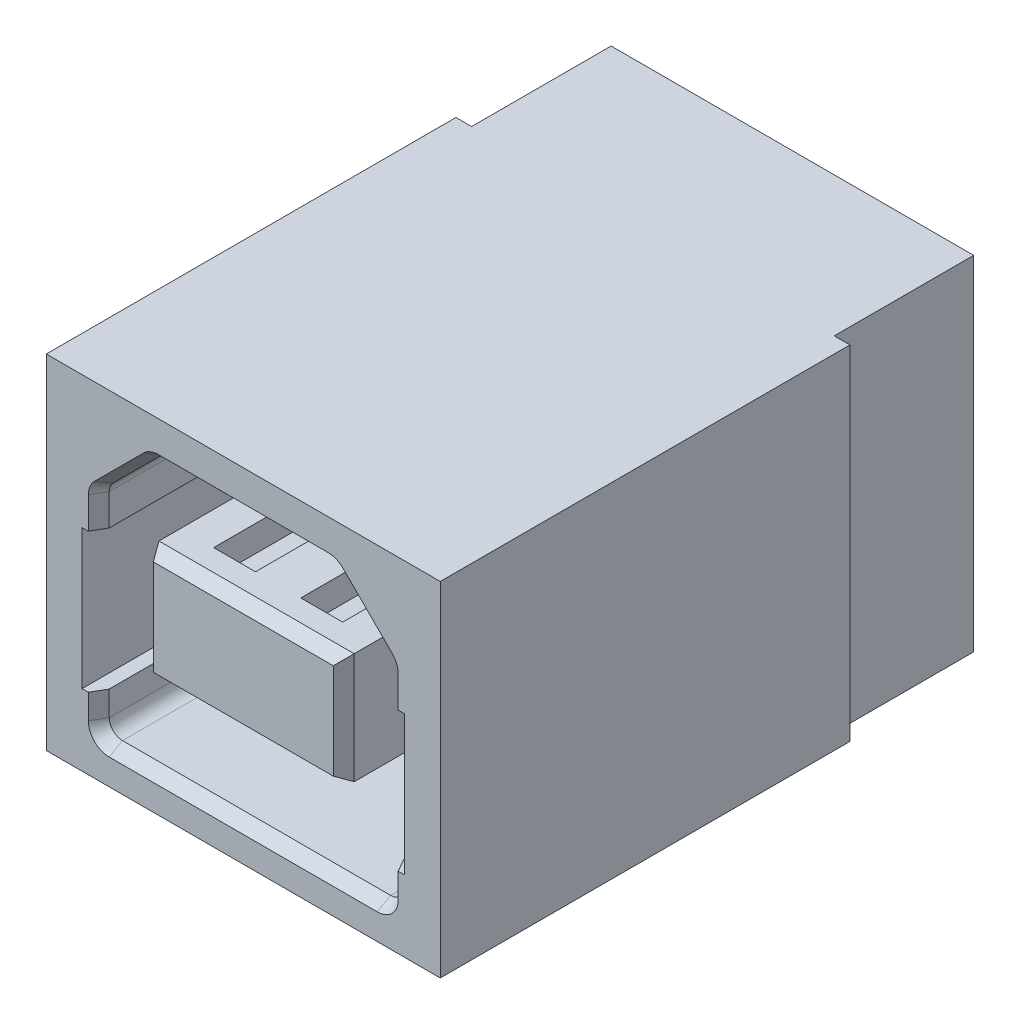
SolidWorks part; units mm, degrees
material "PTFE (general)"
ref_plane "Front Plane" through (0, 0, 0) normal (0, 0, 1) x (1, 0, 0)
ref_plane "Top Plane" through (0, 0, 0) normal (0, 1, 0) x (1, 0, 0)
ref_plane "Right Plane" through (0, 0, 0) normal (1, 0, 0) x (0, 0, -1)
ref_plane "Plane1" through (0, 0, -0.38) normal (0, 0, 1) x (1, 0, 0)
sketch "Sketch1" plane through (0, 0, -0.38) normal (0, 0, 1) x (1, 0, 0)
  line L0 (55, 0) -> (-55, 0) construction
  line L1 (-5.65, 10.25) -> (5.65, 10.25)
  line L2 (-5.65, 10.25) -> (-5.65, 0.4)
  line L3 (-5.65, 0.4) -> (5.65, 0.4)
  line L4 (5.65, 10.25) -> (5.65, 0.4)
  line L5 (0, -55) -> (0, 55) construction
  dimension "D1" = 11.3
  dimension "D2" = 10.25
  dimension "D3" = 0.4
  dimension "D4" = 5.65
extrude "Boss-Extrude1" add sketch "Sketch1" against normal blind 15.75
sketch "Sketch2" plane through (0, 10.25, 0) normal (0, 1, 0) x (1, 0, 0)
  line L0 (0, -55) -> (0, 55) construction
  line L1 (-5.65, 16.13) -> (-5.2, 16.13)
  line L2 (-5.65, 16.13) -> (-5.65, 12.13)
  line L3 (-5.65, 12.13) -> (-5.2, 12.13)
  line L4 (-5.2, 16.13) -> (-5.2, 12.13)
  line L5 (5.65, 16.13) -> (5.2, 16.13)
  line L6 (5.65, 16.13) -> (5.65, 12.13)
  line L7 (5.65, 12.13) -> (5.2, 12.13)
  line L8 (5.2, 16.13) -> (5.2, 12.13)
  dimension "D1" = 10.4
  dimension "D2" = 5.2
  dimension "D3" = 4
extrude "Cut-Extrude1" cut sketch "Sketch2" against normal blind 15.75
sketch "Sketch3" plane through (0, 0, -0.38) normal (0, 0, 1) x (1, 0, 0)
  line L0 (-5.65, 4.45) -> (5.65, 4.45) construction
  line L1 (-5.65, 10.25) -> (-5.65, 0.4) construction
  line L2 (5.65, 0.4) -> (5.65, 10.25) construction
  line L3 (55, 0) -> (-55, 0) construction
  line L4 (-4.225, 7.3526) -> (-4.225, 6.45)
  line L5 (-3.845, 1.36) -> (3.845, 1.36)
  line L6 (4.225, 1.74) -> (4.225, 2.45)
  line L7 (4.1137, 7.6213) -> (2.7063, 9.0287)
  line L8 (2.4376, 9.14) -> (-2.4376, 9.14)
  line L9 (-2.7063, 9.0287) -> (-4.1137, 7.6213)
  line L10 (0, -55) -> (0, 55) construction
  line L11 (-2.8, 5.25) -> (2.8, 5.25) construction
  line L12 (-2.8, 6.84) -> (2.8, 6.84)
  line L13 (-2.8, 6.84) -> (-2.8, 3.66)
  line L14 (-2.8, 3.66) -> (2.8, 3.66)
  line L15 (2.8, 6.84) -> (2.8, 3.66)
  line L16 (-4.225, 2.45) -> (-4.225, 1.74)
  line L17 (4.225, 6.45) -> (4.625, 6.45)
  line L19 (4.225, 2.45) -> (4.625, 2.45)
  line L20 (4.625, 6.45) -> (4.625, 2.45)
  line L21 (-4.225, 6.45) -> (-4.625, 6.45)
  line L22 (4.225, 6.45) -> (4.225, 7.3526)
  line L23 (-4.225, 2.45) -> (-4.625, 2.45)
  line L24 (-4.625, 6.45) -> (-4.625, 2.45)
  arc A0 (-4.225, 7.3526) -> (-4.1137, 7.6213) centre (-3.845, 7.3526) cw
  arc A1 (-2.4376, 9.14) -> (-2.7063, 9.0287) centre (-2.4376, 8.76) ccw
  arc A2 (2.7063, 9.0287) -> (2.4376, 9.14) centre (2.4376, 8.76) ccw
  arc A3 (4.225, 7.3526) -> (4.1137, 7.6213) centre (3.845, 7.3526) ccw
  arc A4 (3.845, 1.36) -> (4.225, 1.74) centre (3.845, 1.74) ccw
  arc A5 (-4.225, 1.74) -> (-3.845, 1.36) centre (-3.845, 1.74) ccw
  point P24 (-4.225, 7.51)
  point P31 (4.225, 7.51)
  dimension "D16" = 0.38
  dimension "D2" = 135
  dimension "D3" = 4.225
  dimension "D4" = 8.45
  dimension "D5" = 7.78
  dimension "D6" = 1.63
  dimension "D7" = 5.6
  dimension "D8" = 2.8
  dimension "D9" = 3.18
  dimension "D10" = 0.8
  dimension "D11" = 5.25
  dimension "D12" = 4.45
  dimension "D13" = 2.3
  dimension "D14" = 2.3
  dimension "D15" = 1.36
  dimension "D17" = 0.4
  dimension "D18" = 4
  dimension "D19" = 2
extrude "Cut-Extrude2" cut sketch "Sketch3" against normal blind 8.38
chamfer "Chamfer1" distance 0.38 angle 30 4 edges at (0, 3.66, -0.38) (2.8, 5.25, -0.38) (0, 6.84, -0.38) (-2.8, 5.25, -0.38)
chamfer "Chamfer2" distance 0.38 angle 30 14 edges at (4.225, 2.095, -0.38) (4.1137, 1.4713, -0.38) (0, 1.36, -0.38) (-4.1137, 1.4713, -0.38) (-4.225, 2.095, -0.38) (4.225, 6.9013, -0.38) (4.1961, 7.498, -0.38) (3.41, 8.325, -0.38) (2.583, 9.1111, -0.38) (0, 9.14, -0.38) (-2.583, 9.1111, -0.38) (-3.41, 8.325, -0.38) (-4.1961, 7.498, -0.38) (-4.225, 6.9013, -0.38)
sketch "Sketch4" plane through (0, 0.4, 0) normal (0, -1, 0) x (-1, 0, 0)
  line L0 (5.2, 16.13) -> (-5.2, 16.13) construction
  line L1 (4.25, 6) -> (3.25, 6)
  line L2 (4.25, 6) -> (4.25, 16.13)
  line L3 (4.25, 16.13) -> (3.25, 16.13)
  line L4 (3.25, 6) -> (3.25, 16.13)
  line L5 (-5.4175, 0) -> (5.4175, 0) construction
  line L6 (0.5, 7.5) -> (-0.5, 7.5)
  line L7 (0.5, 7.5) -> (0.5, 16.13)
  line L8 (0.5, 16.13) -> (-0.5, 16.13)
  line L9 (-0.5, 7.5) -> (-0.5, 16.13)
  line L10 (-3.25, 6) -> (-4.25, 6)
  line L11 (-3.25, 6) -> (-3.25, 16.13)
  line L12 (-3.25, 16.13) -> (-4.25, 16.13)
  line L13 (-4.25, 6) -> (-4.25, 16.13)
  line L14 (0, 5.4175) -> (0, -5.4175) construction
  dimension "D1" = 1
  dimension "D2" = 6
  dimension "D3" = 0.5
  dimension "D4" = 8.5
  dimension "D5" = 4.25
  dimension "D6" = 1.5
extrude "Boss-Extrude2" add sketch "Sketch4" along normal blind 0.83
ref_plane "Plane2" through (0, 0, -1.38) normal (0, 0, 1) x (1, 0, 0)
sketch "Sketch5" plane through (0, 0, -1.38) normal (0, 0, 1) x (1, 0, 0)
  line L0 (-2.8, 6.84) -> (2.8, 6.84) construction
  line L1 (-1.85, 6.84) -> (-0.65, 6.84)
  line L2 (-1.85, 6.84) -> (-1.85, 6.09)
  line L3 (-1.85, 6.09) -> (-0.65, 6.09)
  line L4 (-0.65, 6.84) -> (-0.65, 6.09)
  line L5 (-2.8, 3.66) -> (2.8, 3.66) construction
  line L6 (0.65, 6.84) -> (1.85, 6.84)
  line L7 (0.65, 6.84) -> (0.65, 6.09)
  line L8 (0.65, 6.09) -> (1.85, 6.09)
  line L9 (1.85, 6.84) -> (1.85, 6.09)
  line L10 (0.65, 3.66) -> (1.85, 3.66)
  line L11 (0.65, 3.66) -> (0.65, 4.41)
  line L12 (0.65, 4.41) -> (1.85, 4.41)
  line L13 (1.85, 3.66) -> (1.85, 4.41)
  line L14 (2.8, 3.66) -> (-2.8, 3.66) construction
  line L15 (-1.85, 3.66) -> (-0.65, 3.66)
  line L16 (-1.85, 3.66) -> (-1.85, 4.41)
  line L17 (-1.85, 4.41) -> (-0.65, 4.41)
  line L18 (-0.65, 3.66) -> (-0.65, 4.41)
  line L20 (-1.25, 6.84) -> (-1.25, 3.66) construction
  line L21 (1.25, 6.84) -> (1.25, 3.66) construction
  line L22 (0, -5.874) -> (0, 5.874) construction
  dimension "D1" = 1.2
  dimension "D2" = 1.25
  dimension "D3" = 1.25
  dimension "D4" = 0.75
extrude "Cut-Extrude3" cut sketch "Sketch5" against normal through all
sketch "Sketch6" plane through (0, 0, -16.13) normal (0, 0, -1) x (-1, 0, 0)
  line L0 (-0.5, 0.4) -> (-3.25, 0.4) construction
  line L1 (-1.85, 6.84) -> (-0.65, 6.84)
  line L2 (-1.85, 6.84) -> (-1.85, 0.4)
  line L3 (-1.85, 0.4) -> (-0.65, 0.4)
  line L4 (-0.65, 6.84) -> (-0.65, 0.4)
  line L5 (-0.65, 6.84) -> (-0.65, 6.09) construction
  line L6 (0.65, 6.84) -> (1.85, 6.84)
  line L7 (0.65, 6.84) -> (0.65, 0.4)
  line L8 (0.65, 0.4) -> (1.85, 0.4)
  line L9 (1.85, 6.84) -> (1.85, 0.4)
  line L10 (1.85, 6.84) -> (1.85, 6.09) construction
  line L11 (3.25, 0.4) -> (0.5, 0.4) construction
extrude "Cut-Extrude4" cut sketch "Sketch6" against normal blind 1.29
sketch "Sketch7" plane through (0, 0, -14.84) normal (0, 0, -1) x (-1, 0, 0)
  line L0 (-0.65, 0.4) -> (-0.65, 3.66) construction
  line L1 (1.85, 3.66) -> (0.65, 3.66) construction
  line L2 (-1.55, 2.66) -> (-1.55, 0)
  line L3 (-1.55, 0) -> (-0.95, 0)
  line L4 (-0.95, 2.66) -> (-0.95, 0)
  line L5 (-0.95, 2.66) -> (-0.65, 2.66)
  line L6 (0.95, 2.66) -> (0.95, 0)
  line L7 (0.95, 0) -> (1.55, 0)
  line L8 (1.55, 2.66) -> (1.55, 0)
  line L12 (1.85, 6.84) -> (1.85, 0.4) construction
  line L13 (0.65, 4.41) -> (1.85, 4.41)
  line L14 (0.65, 4.41) -> (0.65, 2.66)
  line L15 (0.65, 2.66) -> (0.95, 2.66)
  line L16 (1.85, 4.41) -> (1.85, 2.66)
  line L17 (-1.85, 0.4) -> (-1.85, 6.84) construction
  line L18 (-1.85, 4.41) -> (-0.65, 4.41)
  line L19 (-1.85, 4.41) -> (-1.85, 2.66)
  line L20 (-1.85, 2.66) -> (-1.55, 2.66)
  line L21 (-0.65, 4.41) -> (-0.65, 2.66)
  line L22 (1.55, 2.66) -> (1.85, 2.66)
  line L23 (-1.85, 4.41) -> (-0.65, 4.41) construction
  dimension "D1" = 0.3
  dimension "D2" = 0.6
  dimension "D3" = 2.5
  dimension "D4" = 2.66
  dimension "D5" = 1
extrude "Cut-Extrude5" cut sketch "Sketch7" against normal blind 2
